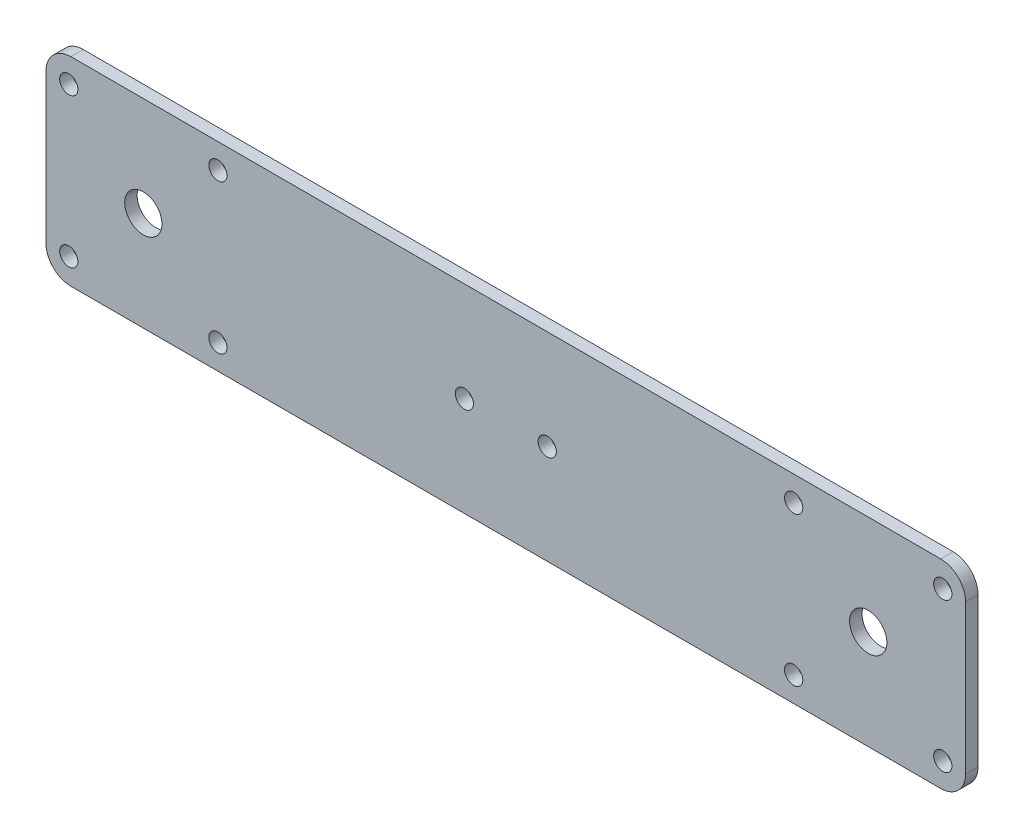
SolidWorks part; units mm, degrees
ref_plane "Plan de face" through (0, 0, 0) normal (0, 0, 1) x (1, 0, 0)
ref_plane "Plan de dessus" through (0, 0, 0) normal (0, 1, 0) x (1, 0, 0)
ref_plane "Plan de droite" through (0, 0, 0) normal (1, 0, 0) x (0, 0, -1)
sketch "Esquisse1" plane through (0, 0, 0) normal (0, 0, 1) x (1, 0, 0)
  line L0 (13, 166) -> (13, 0) construction
  line L1 (0, 0) -> (366, 0)
  line L2 (0, 0) -> (0, 166)
  line L3 (0, 166) -> (366, 166)
  line L4 (366, 0) -> (366, 166)
  line L5 (183, 166) -> (183, 83) construction
  line L6 (183, 83) -> (366, 83) construction
  line L7 (0, 153) -> (366, 153) construction
  line L8 (353, 166) -> (353, 0) construction
  line L9 (0, 13) -> (366, 13) construction
  line L10 (353, 166) -> (353, 0) construction
  line L11 (37, 49) -> (61, 49) construction
  line L12 (77.5, 101) -> (113.5, 101) construction
  line L13 (77.5, 101) -> (77.5, 65) construction
  line L14 (77.5, 65) -> (113.5, 65) construction
  line L15 (113.5, 101) -> (113.5, 65) construction
  line L16 (77.5, 101) -> (113.5, 65) construction
  line L17 (77.5, 65) -> (113.5, 101) construction
  circle A0 centre (13, 153) radius 2.2
  circle A1 centre (13, 13) radius 2.2
  circle A2 centre (13, 83) radius 2.2
  circle A3 centre (173, 153) radius 2.2
  circle A4 centre (193, 83) radius 2.2
  circle A5 centre (173, 83) radius 2.2
  circle A6 centre (193, 153) radius 2.2
  circle A7 centre (353, 83) radius 2.2
  circle A8 centre (353, 13) radius 2.2
  circle A9 centre (353, 153) radius 2.2
  circle A10 centre (193, 13) radius 2.2
  circle A11 centre (173, 13) radius 2.2
  circle A12 centre (270.5, 83) radius 4.5
  circle A13 centre (95.5, 83) radius 4.5
  circle A14 centre (77.5, 101) radius 2.2
  circle A15 centre (113.5, 101) radius 2.2
  circle A16 centre (77.5, 65) radius 2.2
  circle A17 centre (113.5, 65) radius 2.2
  circle A18 centre (288.5, 65) radius 2.2
  circle A19 centre (252.5, 65) radius 2.2
  circle A20 centre (252.5, 101) radius 2.2
  circle A21 centre (288.5, 101) radius 2.2
  circle A22 centre (37, 49) radius 6.5
  circle A23 centre (61, 49) radius 6.5
  circle A24 centre (85, 49) radius 2.2
  circle A25 centre (13, 49) radius 2.2
  point P68 (0, 0)
  dimension "D5" = 4.4
  dimension "D8" = 9
  dimension "D11" = 4.4
  dimension "D12" = 13
  dimension "D16" = 4.4
  dimension "D1" = 366
  dimension "D2" = 166
  dimension "D3" = 13
  dimension "D4" = 13
  dimension "D6" = 10
  dimension "D7" = 10
  dimension "D9" = 175
  dimension "D10" = 36
  dimension "D13" = 36
  dimension "D14" = 24
  dimension "D15" = 24
  dimension "D17" = 24
extrude "Boss.-Extru.1" add sketch "Esquisse1" along normal blind 3
sketch "Esquisse2" plane through (0, 0, 3) normal (0, 0, 1) x (1, 0, 0)
  line L0 (183, 166) -> (183, 0) construction
  line L1 (366, 166) -> (0, 166) construction
  line L2 (0, 0) -> (366, 0) construction
  line L4 (294, 107) -> (72, 107)
  line L5 (294, 107) -> (294, 59)
  line L6 (294, 59) -> (72, 59)
  line L7 (72, 107) -> (72, 59)
  line L8 (294, 107) -> (72, 59) construction
  line L9 (294, 59) -> (72, 107) construction
  point P6 (183, 83)
  dimension "D1" = 48
  dimension "D2" = 222
extrude "Enlèv. mat.-Extru.1" cut sketch "Esquisse2" against normal through all flip side to cut
fillet "Congé1" radius 6 4 edges at (294, 59, 1.5) (294, 107, 1.5) (72, 59, 1.5) (72, 107, 1.5)
